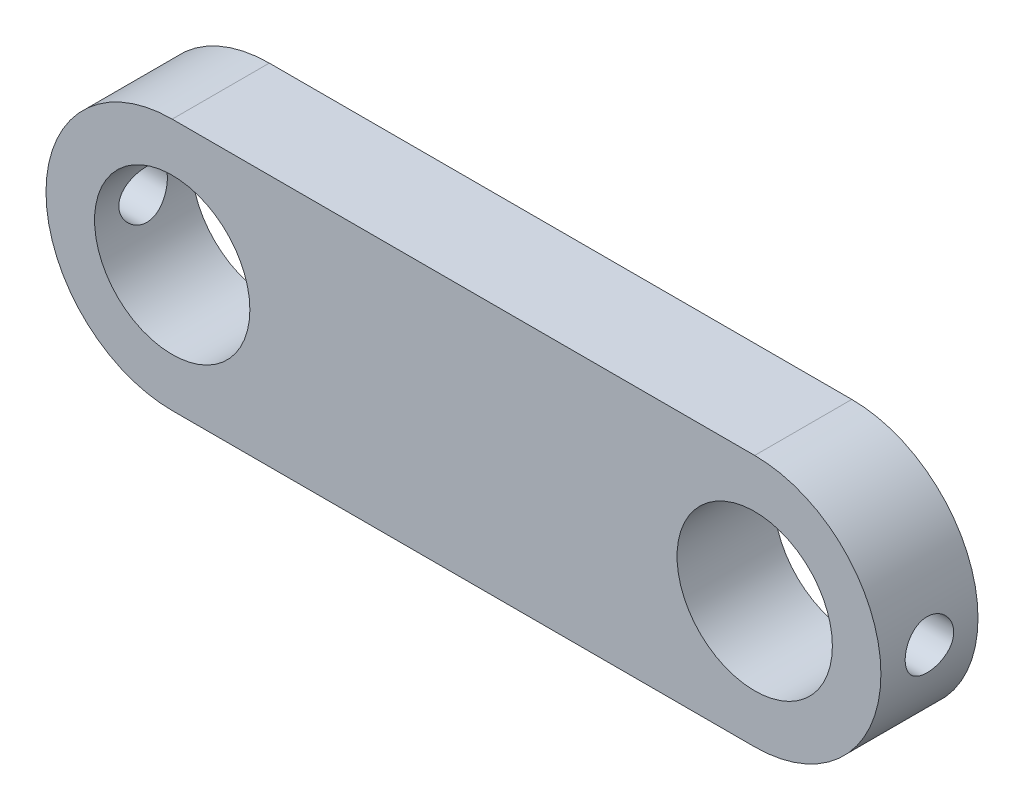
SolidWorks part; units mm, degrees
ref_plane "Front Plane" through (0, 0, 0) normal (0, 0, 1) x (1, 0, 0)
ref_plane "Top Plane" through (0, 0, 0) normal (0, 1, 0) x (1, 0, 0)
ref_plane "Right Plane" through (0, 0, 0) normal (1, 0, 0) x (0, 0, -1)
sketch "Sketch1" plane through (0, 0, 0) normal (0, 0, 1) x (1, 0, 0)
  line L0 (-15, 0) -> (15, 0) construction
  line L3 (-15, 6.5) -> (15, 6.5)
  line L4 (-15, -6.5) -> (15, -6.5)
  arc A2 (15, -6.5) -> (15, 6.5) centre (15, 0) ccw
  arc A3 (-15, 6.5) -> (-15, -6.5) centre (-15, 0) ccw
  circle A4 centre (-15, 0) radius 4
  circle A5 centre (15, 0) radius 4
  point P4 (0, 0)
extrude "Boss-Extrude1" add sketch "Sketch1" along normal blind 5
ref_plane "Plane1" through (21.5, 0, 0) normal (1, 0, 0) x (0, 0, -1)
sketch "Sketch2" plane through (21.5, 0, 0) normal (1, 0, 0) x (0, 0, -1)
  line L0 (0, 0) -> (-5, 0)
  line L1 (-5, 6.5) -> (-5, -6.5) construction
  circle A0 centre (-2.5, 0) radius 1.25
extrude "Cut-Extrude1" cut sketch "Sketch2" against normal blind 5 contours L0 A0 | L0 A0
mirror "Mirror1" about plane through (0, 0, 0) normal (1, 0, 0) of "Cut-Extrude1"
